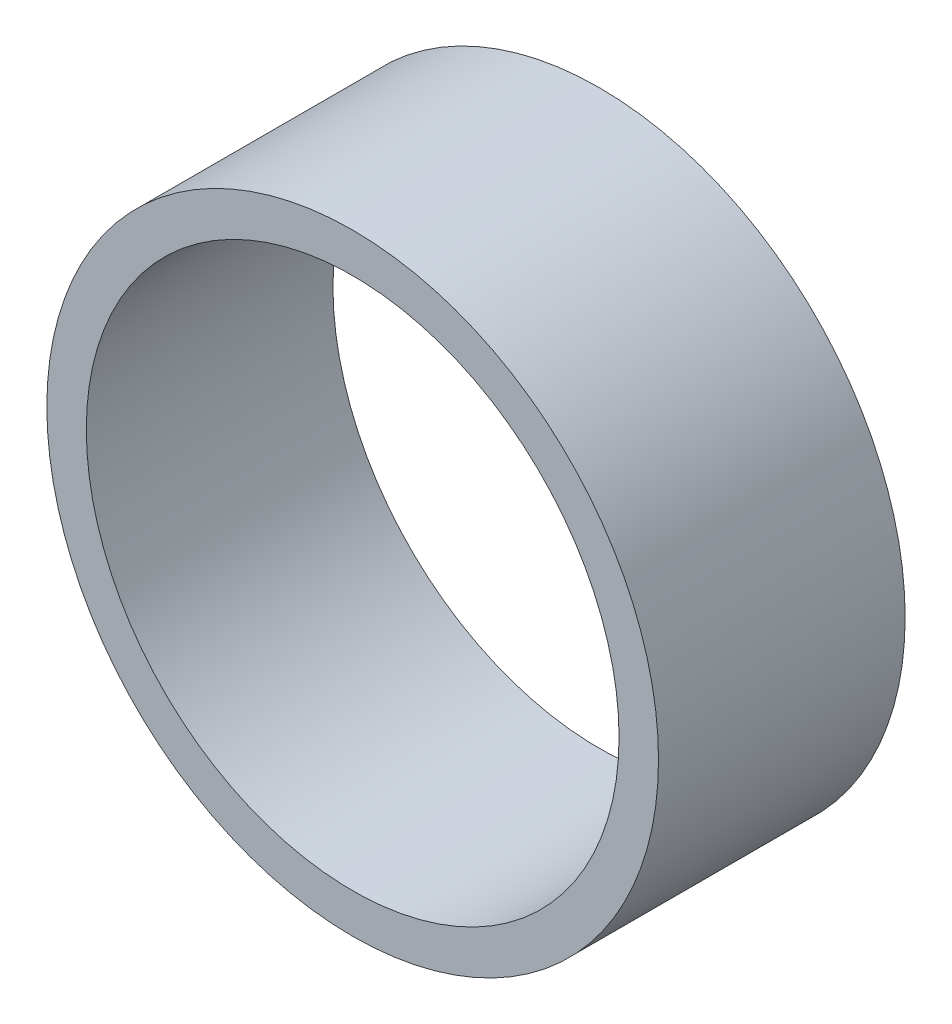
SolidWorks part; units mm, degrees
ref_plane "Front" through (0, 0, 0) normal (0, 0, 1) x (1, 0, 0)
ref_plane "Top" through (0, 0, 0) normal (0, 1, 0) x (1, 0, 0)
ref_plane "Right" through (0, 0, 0) normal (1, 0, 0) x (0, 0, -1)
sketch "Esquisse1" plane through (0, 0, 0) normal (0, 0, 1) x (1, 0, 0)
  circle A0 centre (0, 0) radius 27
  circle A1 centre (0, 0) radius 31
  dimension "D1" = 54
  dimension "D2" = 62
extrude "Boss.-Extru.1" add sketch "Esquisse1" along normal blind 25
